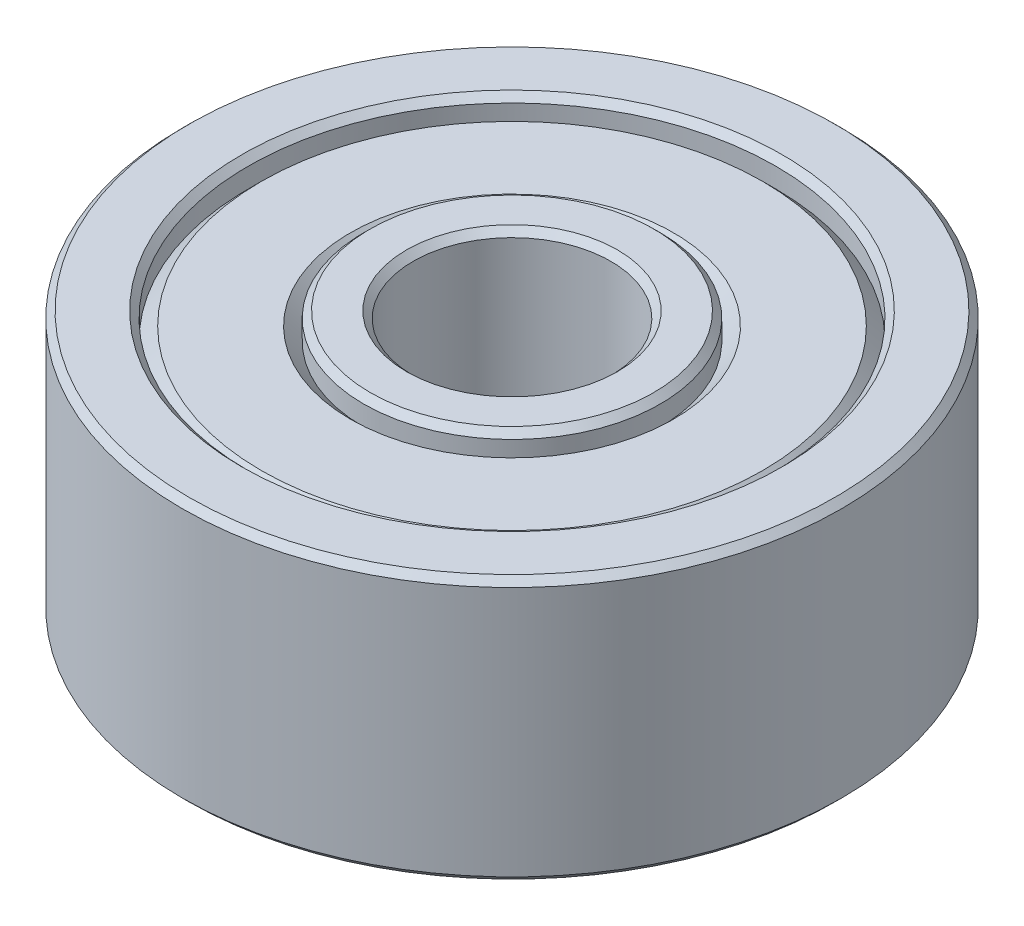
SolidWorks part; units mm, degrees
ref_plane "Front Plane" through (0, 0, 0) normal (0, 0, 1) x (1, 0, 0)
ref_plane "Top Plane" through (0, 0, 0) normal (0, 1, 0) x (1, 0, 0)
ref_plane "Right Plane" through (0, 0, 0) normal (1, 0, 0) x (0, 0, -1)
sketch "Sketch1" plane through (0, 0, 0) normal (1, 0, 0) x (0, 0, -1)
  line L1 (0, 2) -> (5, 2)
  line L2 (0, 2) -> (0, -2) construction
  line L3 (0, -2) -> (5, -2)
  line L4 (5, 2) -> (5, -2)
  line L6 (3.6, 0) -> (0, 0) construction
  line L7 (1.5, 2) -> (1.5, -2)
  dimension "D1" = 4
  dimension "D2" = 5
  dimension "D3" = 1.4
  dimension "D5" = 3
revolve "Revolve1" add sketch "Sketch1" angle 360 about L2
sketch "Sketch3" plane through (0, 0, 0) normal (1, 0, 0) x (0, 0, -1)
  line L0 (5, 2) -> (5, -2) construction
  line L1 (1.5, 2) -> (1.5, -2) construction
  line L2 (0, 2) -> (5, 2) construction
  line L3 (5, 2) -> (5, -2) construction
  line L4 (1.5, 2) -> (1.5, -2)
  line L5 (0, 2) -> (5, 2) construction
  line L6 (2.25, 2) -> (4, 2)
  line L7 (2.25, 2) -> (2.25, 1.6)
  line L8 (2.25, 1.6) -> (2.45, 1.8)
  line L9 (2.45, 1.8) -> (3.8, 1.8)
  line L10 (3.8, 1.8) -> (4, 1.6)
  line L11 (4, 1.6) -> (4, 2)
  line L14 (0, 2) -> (0, -2) construction
  line L17 (0, 2) -> (0, -2) construction
  line L18 (2.25, 1.6) -> (4, 1.6) construction
  line L19 (3.125, 1.6) -> (3.125, 2) construction
  dimension "D1" = 1
  dimension "D2" = 0.2
  dimension "D3" = 0.75
  dimension "D4" = 0.2
  dimension "D5" = 0.2
revolve "Cut-Revolve2" cut sketch "Sketch3" angle 360 about L17
mirror "Mirror1" about plane through (0, 0, 0) normal (0, 1, 0) of "Cut-Revolve2"
chamfer "Chamfer1" distance 0.1 angle 45 8 edges at (0, -2, 4) (0, 2, 4) (0, -2, 5) (0, 2, 5) (0, -2, 2.25) (0, 2, 2.25) (0, -2, 1.5) (0, 2, 1.5)
